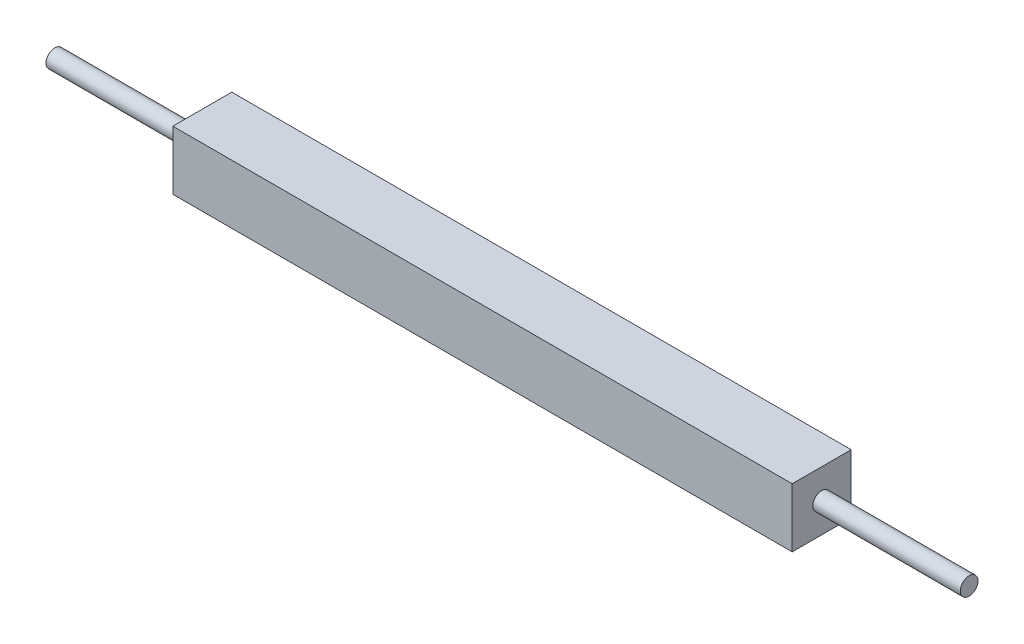
SolidWorks part; units mm, degrees
ref_plane "Front" through (0, 0, 0) normal (0, 0, 1) x (1, 0, 0)
ref_plane "Top" through (0, 0, 0) normal (0, 1, 0) x (1, 0, 0)
ref_plane "Right" through (0, 0, 0) normal (1, 0, 0) x (0, 0, -1)
sketch "Sketch1" plane through (0, 0, 0) normal (0, 0, 1) x (1, 0, 0)
  line L0 (0, 0) -> (0, 20) construction
  line L1 (-210, -20) -> (0, -20)
  line L2 (-210, -20) -> (-210, 20)
  line L3 (-210, 20) -> (0, 20)
  line L5 (-210, -20) -> (0, 0) construction
  line L6 (-210, 20) -> (0, 0) construction
  line L7 (0, 20) -> (0, -20) construction
  line L8 (0, 20) -> (0, -20)
  point P0 (0, 0)
  dimension "D2" = 40
extrude "Boss-Extrude1" add sketch "Sketch1" along normal blind 40
sketch "Sketch2" plane through (-210, 0, 0) normal (-1, 0, 0) x (0, 0, 1)
  line L0 (40, 20) -> (0, -20) construction
  circle A0 centre (20, 0) radius 6
  dimension "D1" = 12
extrude "Boss-Extrude2" add sketch "Sketch2" along normal blind 100
mirror "Mirror1" about plane through (0, 20, 40) normal (-1, 0, 0) of bodies 102
sketch "Sketch3" plane through (0, 0, 40) normal (0, 0, 1) x (1, 0, 0)
  point P6 (5.4166, 34.3133)
  point P7 (-126.6723, 172.9889)
sketch "Sketch4" plane through (0, 0, 40) normal (0, 0, 1) x (1, 0, 0)
  line L0 (-210, 0) -> (210, 0) construction
  line L1 (-210, 20) -> (-210, -20) construction
  line L2 (210, 20) -> (210, -20) construction
  point P6 (0, 0)
